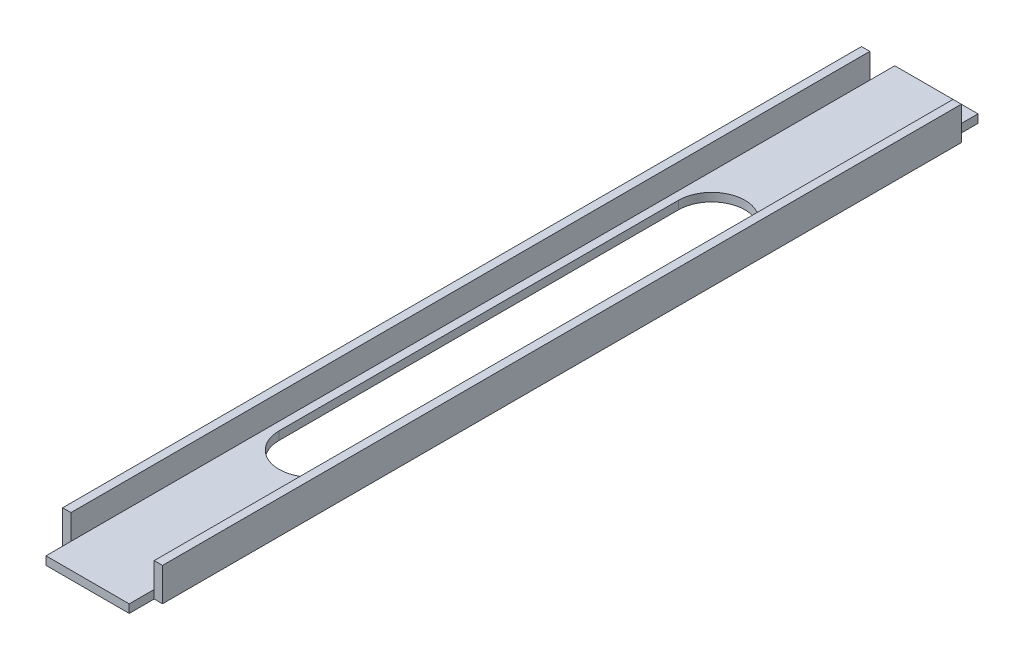
SolidWorks part; units mm, degrees
ref_plane "Front" through (0, 0, 0) normal (0, 0, 1) x (1, 0, 0)
ref_plane "Top" through (0, 0, 0) normal (0, 1, 0) x (1, 0, 0)
ref_plane "Right" through (0, 0, 0) normal (1, 0, 0) x (0, 0, -1)
sketch "Sketch1" plane through (0, 0, 0) normal (0, 0, 1) x (1, 0, 0)
  line L0 (3.175, 3.175) -> (3.175, 12.7)
  line L1 (0, 0) -> (38.1, 0)
  line L2 (0, 0) -> (0, 12.7)
  line L4 (38.1, 0) -> (38.1, 12.7)
  line L5 (3.175, 3.175) -> (34.925, 3.175)
  line L6 (34.925, 3.175) -> (34.925, 12.7)
  line L7 (0, 12.7) -> (3.175, 12.7)
  line L8 (38.1, 12.7) -> (34.925, 12.7)
  dimension "D1" = 12.7
  dimension "D2" = 38.1
  dimension "D3" = 3.175
extrude "Boss-Extrude1" add sketch "Sketch1" along normal blind 323.85
sketch "Sketch2" plane through (0, 0, 0) normal (-1, 0, 0) x (0, 0, 1)
  line L0 (323.85, 12.7) -> (0, 12.7) construction
  line L1 (323.85, 0) -> (314.325, 0)
  line L2 (323.85, 0) -> (323.85, 12.7)
  line L3 (323.85, 12.7) -> (314.325, 12.7)
  line L4 (314.325, 0) -> (314.325, 12.7)
  line L5 (323.85, 0) -> (314.325, 12.7) construction
  line L6 (323.85, 12.7) -> (314.325, 0) construction
  line L7 (161.925, 12.7) -> (161.925, 0) construction
  line L9 (323.85, 0) -> (0, 0) construction
  line L10 (0, 12.7) -> (9.525, 0) construction
  line L15 (0, 0) -> (9.525, 12.7) construction
  line L16 (9.525, 0) -> (9.525, 12.7)
  line L17 (0, 12.7) -> (9.525, 12.7)
  line L18 (0, 0) -> (0, 12.7)
  line L19 (0, 0) -> (9.525, 0)
  point P4 (319.0875, 6.35)
  point P16 (4.7625, 6.35)
  dimension "D1" = 9.525
extrude "Cut-Extrude1" cut sketch "Sketch2" against normal blind 3.175
ref_plane "Plane1" through (19.05, 0, 0) normal (-1, 0, 0) x (0, 0, 1)
mirror "Mirror1" about plane through (19.05, 0, 0) normal (-1, 0, 0) of "Cut-Extrude1"
sketch "Sketch3" plane through (0, 0, 0) normal (0, -1, 0) x (1, 0, 0)
  line L0 (0, 314.325) -> (38.1, 9.525) construction
  line L1 (19.05, 238.125) -> (19.05, 85.725) construction
  line L2 (31.75, 238.125) -> (31.75, 85.725)
  line L3 (6.35, 238.125) -> (6.35, 85.725)
  arc A0 (31.75, 238.125) -> (6.35, 238.125) centre (19.05, 238.125) ccw
  arc A1 (6.35, 85.725) -> (31.75, 85.725) centre (19.05, 85.725) ccw
  point P6 (19.05, 161.925)
  dimension "D1" = 152.4
extrude "Cut-Extrude2" cut sketch "Sketch3" against normal up to next
